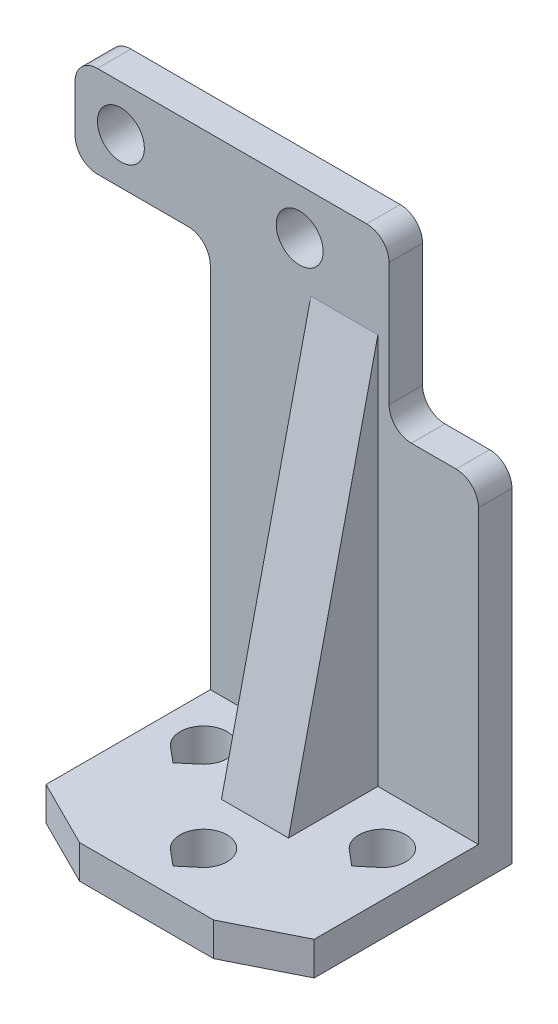
SolidWorks part; units mm, degrees
other "left" parameters "D3"=4.7518, "D4"=4.1, "D5"=4.1, "D6"=5.2924, "D12"=2.1, "D1"=29.1602, "D2"=41.029, "D7"=24, "D8"=24, "D9"=3.8969, "D10"=1.7408, "D11"=1.6897, "D13"=26.823, "D14"=14.4534, "D15"=24
ref_plane "Front Plane" through (0, 0, 0) normal (0, 0, 1) x (1, 0, 0)
ref_plane "Top Plane" through (0, 0, 0) normal (0, 1, 0) x (1, 0, 0)
ref_plane "Right Plane" through (0, 0, 0) normal (1, 0, 0) x (0, 0, -1)
sketch "Sketch1" plane through (0, 0, 0) normal (0, 1, 0) x (1, 0, 0)
  line L0 (0, 0) -> (0, -17.7) construction
  line L2 (-12, -17.7) -> (-12, 0)
  line L3 (-12, 0) -> (12, 0)
  line L4 (12, -17.7) -> (12, 0)
  line L5 (-12, -12.6) -> (12, -12.6) construction
  line L6 (-12, -17.7) -> (12, -17.7)
  line L7 (-9.3499, -6.2087) -> (-8, -7.3414)
  line L8 (-8, -7.3414) -> (-6.6501, -6.2087)
  line L9 (6.6501, -6.2087) -> (8, -7.3414)
  line L10 (8, -7.3414) -> (9.3499, -6.2087)
  line L13 (-1.3499, -14.2087) -> (0, -15.3414)
  line L14 (0, -15.3414) -> (1.3499, -14.2087)
  arc A0 (-6.6501, -6.2087) -> (-9.3499, -6.2087) centre (-8, -4.6) ccw
  arc A1 (9.3499, -6.2087) -> (6.6501, -6.2087) centre (8, -4.6) ccw
  arc A2 (1.3499, -14.2087) -> (-1.3499, -14.2087) centre (0, -12.6) ccw
  point P3 (0, -17.7)
  point P4 (0, 0)
  dimension "D3" = 4.2
  dimension "D6" = 4.2
  dimension "D4" = 16
  dimension "D5" = 16
  dimension "D7" = 3
  dimension "D2" = 24
  dimension "D8" = 100
  dimension "D9" = 100
  dimension "D10" = 100
  dimension "D11" = 50
  dimension "D12" = 2.5
extrude "Boss-Extrude1" add sketch "Sketch1" along normal blind 3
sketch "Sketch2" plane through (0, 0, 0) normal (0, 0, 1) x (1, 0, 0)
  line L1 (12, 0) -> (-12, 0)
  line L2 (12, 0) -> (12, 31.1)
  line L3 (4, 46.1) -> (-12, 46.1)
  line L4 (-12, 0) -> (-12, 37.9)
  line L5 (-12, 46.1) -> (-12, 37.9) construction
  line L7 (-9, 28.1) -> (5.418, 6) construction
  line L8 (-12, 46.1) -> (-24.1, 46.1)
  line L10 (-12, 37.9) -> (-24.1, 37.9)
  line L11 (-24.1, 46.1) -> (-24.1, 37.9)
  line L12 (12, 31.1) -> (4, 31.1)
  line L15 (4, 31.1) -> (4, 46.1)
  line L16 (5.418, 6) -> (-9, 6) construction
  line L17 (-9, 6) -> (-9, 28.1) construction
  line L18 (-5.418, 28.1) -> (9, 6) construction
  line L19 (9, 6) -> (9, 28.1) construction
  line L20 (9, 28.1) -> (-5.418, 28.1) construction
  line L21 (12, 3) -> (-12, 3) construction
  circle A0 centre (-20, 42) radius 2.1
  circle A1 centre (-4, 42) radius 2.1
  dimension "D3" = 4.2
  dimension "D2" = 16
  dimension "D4" = 2
  dimension "D5" = 5.9
  dimension "D6" = 2
  dimension "D7" = 2
  dimension "D8" = 8
  dimension "D9" = 15
  dimension "D10" = 3
  dimension "D11" = 3
  dimension "D13" = 3
  dimension "D14" = 3
  dimension "D15" = 42
  dimension "D12" = 3
extrude "Boss-Extrude2" add sketch "Sketch2" against normal blind 3
sketch "Sketch3" plane through (0, 0, 0) normal (1, 0, 0) x (0, 0, -1)
  line L0 (0, 3) -> (-8, 3)
  line L1 (-17.7, 3) -> (0, 3) construction
  line L2 (-8, 3) -> (0, 38)
  line L3 (0, 3) -> (0, 31.1) construction
  line L4 (0, 38) -> (0, 3)
  dimension "D1" = 8
  dimension "D2" = 35
extrude "Boss-Extrude3" add sketch "Sketch3" along normal mid plane 6
chamfer "Chamfer1" distance 6 distance2 3 1 edges at (12, 1.5, 17.7)
chamfer "Chamfer2" distance 3 distance2 6 1 edges at (-12, 1.5, 17.7)
fillet "Fillet1" radius 2 6 edges at (-12, 37.9, -1.5) (4, 31.1, -1.5) (12, 31.1, -1.5) (4, 46.1, -1.5) (-24.1, 46.1, -1.5) (-24.1, 37.9, -1.5)
fillet "Fillet2" [suppressed] radius 1
equation "\"width\"= 24"
equation "\"thk\"= 3"
equation "\"holesize\"= 4.2"
equation "\"holedistance\"= ( 20 + 12 ) / 2"
equation "\"threaded_hole\"= 3.9"
equation "\"fillet_radius\"= 2"
equation "\"ground_clearance\"= 25"
equation "\"tire_thk\"= 3"
equation "\"innerwheel_diam\" = \"wheel_diam\"-2*\"tire_thk\""
equation "\"innerwheel_thk\"= 8"
equation "\"wheel_diam\"= 2*(\"width\"/2+\"ground_clearance\")"
equation "\"D3@Sketch1\"=\"holesize\""
equation "\"D4@Sketch1\"=\"holedistance\""
equation "\"D5@Sketch1\"=\"holedistance\""
equation "\"D6@Sketch1\"=\"D3@Sketch1\""
equation "\"D1@Boss-Extrude1\"=\"thk\""
equation "\"D1@Boss-Extrude2\"=\"thk\""
equation "\"D2@Sketch2\"=\"holedistance\""
equation "\"D3@Sketch2\"=\"holesize\""
equation "\"D7@Sketch2\"=\"D4@Sketch2\""
equation "\"D6@Sketch2\"=\"D4@Sketch2\""
equation "\"D2@Sketch1\"=\"width\""
equation "\"D1@Fillet1\"=\"fillet_radius\""
equation "\"D9@Sketch1\"=\"D8@Sketch1\""
equation "\"D10@Sketch1\"=\"D8@Sketch1\""
equation "\"coloursensor_holesize\"= 2.65"
equation "\"hole_to_edge\" = 4"
